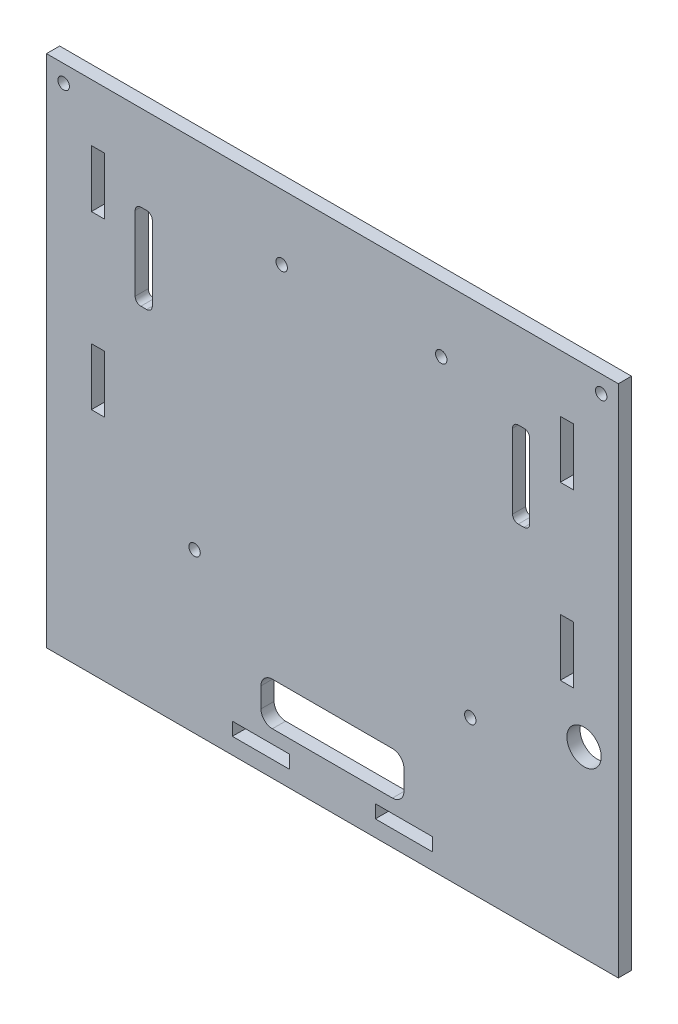
SolidWorks part; units mm, degrees
ref_plane "Front Plane" through (0, 0, 0) normal (0, 0, 1) x (1, 0, 0)
ref_plane "Top Plane" through (0, 0, 0) normal (0, 1, 0) x (1, 0, 0)
ref_plane "Right Plane" through (0, 0, 0) normal (1, 0, 0) x (0, 0, -1)
sketch "Sketch1" plane through (0, 0, 0) normal (0, 0, 1) x (1, 0, 0)
  line L0 (0, -57) -> (0, -90)
  line L1 (0, 0) -> (100, 0)
  line L2 (0, 0) -> (0, -57)
  line L3 (0, -90) -> (23, -90)
  line L4 (100, 0) -> (100, -57)
  line L5 (77, -90) -> (100, -90)
  line L6 (100, -90) -> (100, -57)
  line L7 (0, -57) -> (23, -57) construction
  line L8 (23, -90) -> (23, -57) construction
  line L11 (100, -57) -> (77, -57) construction
  line L12 (77, -90) -> (77, -57) construction
  line L14 (23, -90) -> (77, -90)
  dimension "D1" = 100
  dimension "D2" = 57
  dimension "D3" = 23
  dimension "D4" = 23
  dimension "D5" = 33
  dimension "D6" = 33
  dimension "D7" = 54
extrude "Boss-Extrude1" add sketch "Sketch1" along normal blind 2.3
sketch "Sketch7" plane through (0, 0, 2.3) normal (0, 0, 1) x (1, 0, 0)
  line L0 (100, -90) -> (100, 0) construction
  line L1 (67.5, -84.85) -> (100, -84.85) construction
  line L2 (100, -90) -> (100, 0) construction
  line L3 (89.85, -10) -> (92.15, -10)
  line L4 (89.85, -10) -> (89.85, -20)
  line L5 (89.85, -20) -> (92.15, -20)
  line L6 (92.15, -10) -> (92.15, -20)
  line L7 (89.85, -10) -> (92.15, -20) construction
  line L8 (89.85, -20) -> (92.15, -10) construction
  line L9 (100, 0) -> (0, 0) construction
  line L10 (89.85, -40) -> (92.15, -50) construction
  line L11 (92.15, -40) -> (92.15, -50)
  line L12 (89.85, -40) -> (89.85, -50)
  line L13 (89.85, -50) -> (92.15, -40) construction
  line L14 (89.85, -40) -> (92.15, -40)
  line L15 (89.85, -50) -> (92.15, -50)
  line L16 (7.85, -10) -> (10.15, -10)
  line L17 (7.85, -20) -> (10.15, -10) construction
  line L18 (7.85, -10) -> (7.85, -20)
  line L19 (7.85, -20) -> (10.15, -20)
  line L20 (10.15, -10) -> (10.15, -20)
  line L21 (7.85, -10) -> (10.15, -20) construction
  line L22 (0, 0) -> (0, -90) construction
  line L23 (7.85, -50) -> (10.15, -40) construction
  line L24 (10.15, -40) -> (10.15, -50)
  line L25 (7.85, -50) -> (10.15, -50)
  line L26 (7.85, -40) -> (10.15, -50) construction
  line L27 (7.85, -40) -> (7.85, -50)
  line L28 (7.85, -40) -> (10.15, -40)
  line L29 (0, -90) -> (100, -90) construction
  line L30 (32.5, -87.15) -> (42.5, -87.15)
  line L31 (32.5, -87.15) -> (32.5, -84.85)
  line L32 (32.5, -84.85) -> (42.5, -84.85)
  line L33 (42.5, -87.15) -> (42.5, -84.85)
  line L34 (32.5, -87.15) -> (42.5, -84.85) construction
  line L35 (32.5, -84.85) -> (42.5, -87.15) construction
  line L36 (67.5, -87.15) -> (57.5, -87.15)
  line L37 (67.5, -87.15) -> (67.5, -84.85)
  line L38 (67.5, -84.85) -> (57.5, -84.85)
  line L39 (57.5, -87.15) -> (57.5, -84.85)
  line L40 (67.5, -87.15) -> (57.5, -84.85) construction
  line L41 (67.5, -84.85) -> (57.5, -87.15) construction
  point P0 (91, -15)
  point P7 (9, -15)
  point P11 (91, -45)
  point P21 (9, -45)
  point P26 (37.5, -86)
  point P31 (62.5, -86)
  dimension "D1" = 2.3
  dimension "D2" = 10
  dimension "D3" = 9
  dimension "D4" = 10
  dimension "D5" = 10
  dimension "D6" = 9
  dimension "D7" = 20
  dimension "D8" = 10
  dimension "D9" = 9
  dimension "D10" = 10
  dimension "D11" = 9
  dimension "D12" = 20
  dimension "D13" = 2.3
  dimension "D14" = 2.3
  dimension "D15" = 10
  dimension "D16" = 2.3
  dimension "D17" = 4
  dimension "D18" = 4
  dimension "D19" = 10
  dimension "D20" = 10
  dimension "D21" = 2.3
  dimension "D22" = 2.3
  dimension "D23" = 15
  dimension "D24" = 32.5
extrude "Cut-Extrude2" cut sketch "Sketch7" against normal through all
sketch "Sketch9" plane through (0, 0, 2.3) normal (0, 0, 1) x (1, 0, 0)
  line L0 (100, 0) -> (0, 0) construction
  line L1 (0, 0) -> (0, -90) construction
  line L2 (100, -90) -> (100, 0) construction
  line L4 (0, -90) -> (100, -90) construction
  line L6 (25.89, -62.2) -> (0, -62.2) construction
  line L7 (0, 0) -> (0, -90) construction
  line L8 (74.11, -63.5) -> (100, -63.5) construction
  line L9 (100, -90) -> (100, 0) construction
  circle A0 centre (3, -3) radius 1
  circle A1 centre (97, -3) radius 1
  circle A2 centre (41.13, -11.4) radius 1
  circle A3 centre (69.03, -11.4) radius 1
  circle A4 centre (25.89, -62.2) radius 1
  circle A5 centre (74.11, -63.5) radius 1
  dimension "D1" = 3
  dimension "D3" = 2
  dimension "D4" = 3
  dimension "D6" = 2
  dimension "D7" = 11.4
  dimension "D10" = 2
  dimension "D12" = 2
  dimension "D13" = 25.89
  dimension "D17" = 2
  dimension "D18" = 2
  dimension "D2" = 3
  dimension "D5" = 3
  dimension "D8" = 11.4
  dimension "D9" = 41.13
  dimension "D11" = 30.97
  dimension "D14" = 26.5
  dimension "D15" = 25.89
  dimension "D16" = 27.8
extrude "Cut-Extrude4" cut sketch "Sketch9" against normal through all
sketch "Sketch10" plane through (0, 0, 2.3) normal (0, 0, 1) x (1, 0, 0)
  line L0 (100, 0) -> (0, 0) construction
  line L1 (15.5, -15) -> (18.5, -15)
  line L2 (15.5, -15) -> (15.5, -30)
  line L3 (15.5, -30) -> (18.5, -30)
  line L4 (18.5, -15) -> (18.5, -30)
  line L5 (0, 0) -> (0, -90) construction
  line L6 (100, -90) -> (100, 0) construction
  line L7 (81.5, -15) -> (84.5, -15)
  line L8 (81.5, -15) -> (81.5, -30)
  line L9 (81.5, -30) -> (84.5, -30)
  line L10 (84.5, -15) -> (84.5, -30)
  line L12 (37.5, -75) -> (62.5, -75)
  line L13 (37.5, -75) -> (37.5, -82.5)
  line L14 (37.5, -82.5) -> (62.5, -82.5)
  line L15 (62.5, -75) -> (62.5, -82.5)
  line L16 (0, -90) -> (100, -90) construction
  line L17 (62.5, -75) -> (100, -75) construction
  line L18 (100, -90) -> (100, 0) construction
  dimension "D1" = 3
  dimension "D2" = 15
  dimension "D3" = 15
  dimension "D4" = 15.5
  dimension "D5" = 3
  dimension "D6" = 15
  dimension "D7" = 15.5
  dimension "D8" = 15
  dimension "D9" = 25
  dimension "D10" = 7.5
  dimension "D11" = 37.5
  dimension "D12" = 7.5
extrude "Cut-Extrude5" cut sketch "Sketch10" against normal through all
fillet "Fillet2" radius 1 8 edges at (84.5, -30, 1.15) (81.5, -30, 1.15) (81.5, -15, 1.15) (84.5, -15, 1.15) (18.5, -30, 1.15) (18.5, -15, 1.15) (15.5, -15, 1.15) (15.5, -30, 1.15)
fillet "Fillet3" radius 2 4 edges at (62.5, -82.5, 1.15) (62.5, -75, 1.15) (37.5, -82.5, 1.15) (37.5, -75, 1.15)
sketch "Sketch11" plane through (0, 0, 2.3) normal (0, 0, 1) x (1, 0, 0)
  line L0 (100, -90) -> (94, -90) construction
  line L1 (0, -90) -> (100, -90) construction
  line L2 (94, -90) -> (94, -58) construction
  circle A0 centre (94, -58) radius 3
  dimension "D3" = 6
  dimension "D1" = 6
  dimension "D2" = 32
extrude "Cut-Extrude6" cut sketch "Sketch11" against normal blind 10
